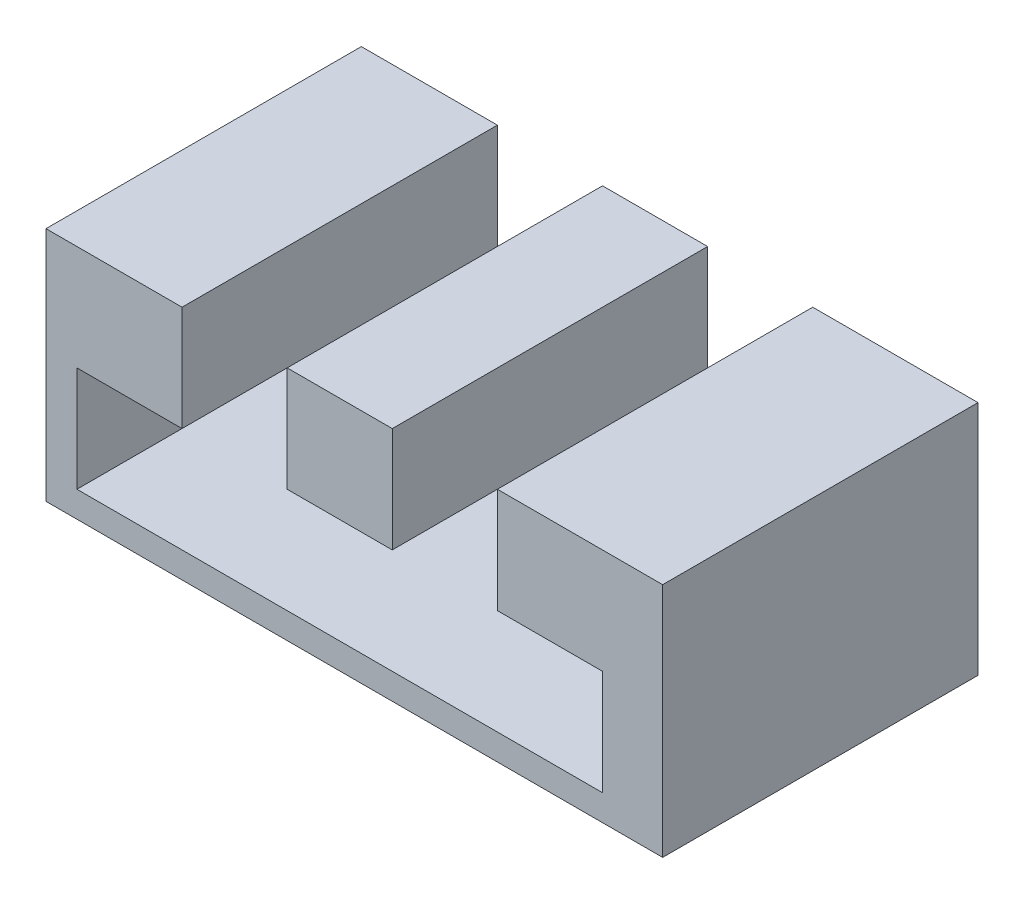
SolidWorks part; units mm, degrees
ref_plane "Front Plane" through (0, 0, 0) normal (0, 0, 1) x (1, 0, 0)
ref_plane "Top Plane" through (0, 0, 0) normal (0, 1, 0) x (1, 0, 0)
ref_plane "Right Plane" through (0, 0, 0) normal (1, 0, 0) x (0, 0, -1)
sketch "Sketch2" plane through (0, 0, 0) normal (0, 0, 1) x (1, 0, 0)
  line L0 (0, 0) -> (50, 0)
  line L1 (50, 0) -> (50, 10)
  line L2 (50, 10) -> (40, 10)
  line L3 (40, 10) -> (40, 20)
  line L4 (40, 20) -> (30, 20)
  line L5 (30, 20) -> (30, 10)
  line L6 (30, 10) -> (20, 10)
  line L7 (20, 10) -> (20, 20)
  line L8 (20, 20) -> (10, 20)
  line L9 (10, 20) -> (10, 10)
  line L10 (10, 10) -> (0, 10)
  line L11 (0, 10) -> (0, 0)
  dimension "D1" = 10
sketch "Sketch3" plane through (0, 0, 0) normal (0, 0, 1) x (1, 0, 0)
  line L1 (-2.9432, -2.4718) -> (55.7217, -2.4718)
  line L2 (-2.9432, -2.4718) -> (-2.9432, 20)
  line L3 (-2.9432, 20) -> (55.7217, 20)
  line L4 (55.7217, -2.4718) -> (55.7217, 20)
  line L5 (20, 20) -> (10, 20) construction
extrude "Boss-Extrude2" add sketch "Sketch3" along normal blind 30
extrude "Cut-Extrude1" cut sketch "Sketch2" along normal through all
